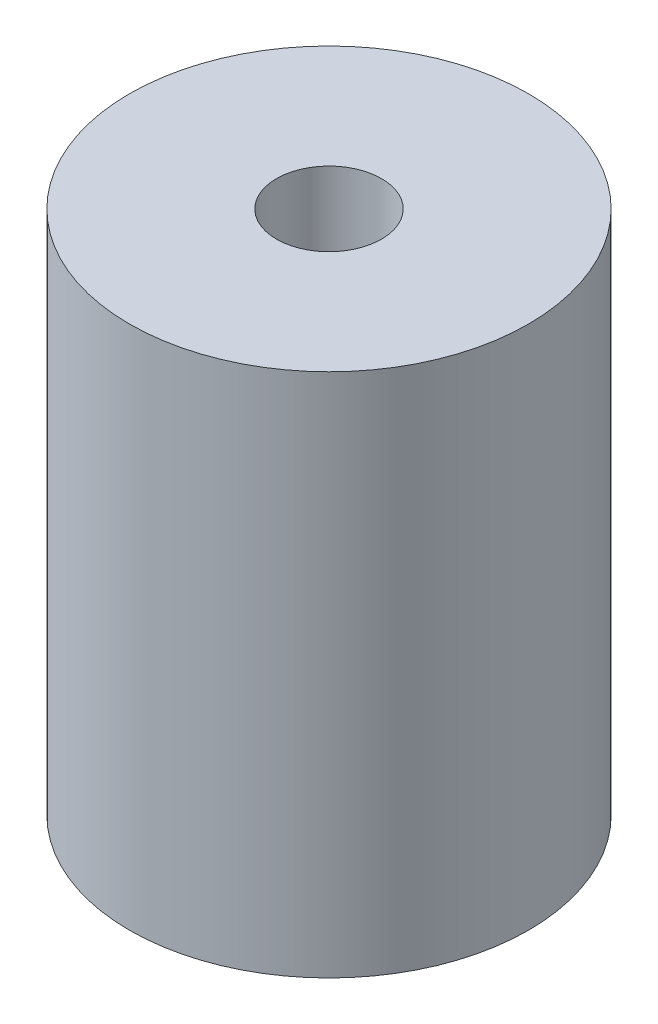
SolidWorks part; units mm, degrees
material "5052-H32"
ref_plane "Front Plane" through (0, 0, 0) normal (0, 0, 1) x (1, 0, 0)
ref_plane "Top Plane" through (0, 0, 0) normal (0, 1, 0) x (1, 0, 0)
ref_plane "Right Plane" through (0, 0, 0) normal (1, 0, 0) x (0, 0, -1)
sketch "Sketch1" plane through (0, 0, 0) normal (0, 1, 0) x (1, 0, 0)
  circle A0 centre (0, 0) radius 9.5
  dimension "D1" = 19
extrude "Boss-Extrude1" add sketch "Sketch1" along normal blind 25
sketch "Sketch2" plane through (0, 0, 0) normal (0, -1, 0) x (1, 0, 0)
  circle A0 centre (0, 0) radius 5
  circle A1 centre (0, 0) radius 9.5 construction
  dimension "D1" = 10
extrude "Cut-Extrude1" cut sketch "Sketch2" against normal blind 10 contours A0
sketch "Sketch3" plane through (0, 25, 0) normal (0, 1, 0) x (1, 0, 0)
  circle A0 centre (0, 0) radius 2.5
  dimension "D1" = 5
extrude "Cut-Extrude2" cut sketch "Sketch3" against normal through all
